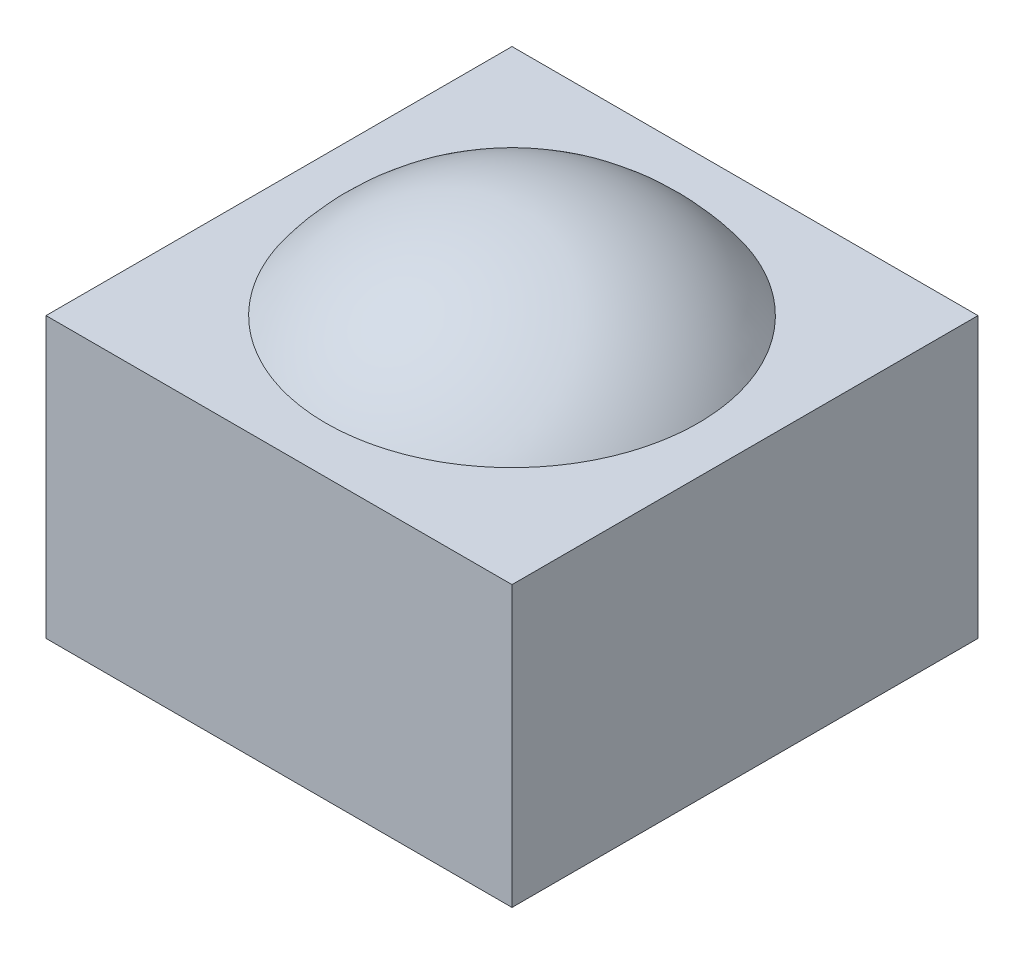
SolidWorks part; units mm, degrees
ref_plane "Ebene vorne" through (0, 0, 0) normal (0, 0, 1) x (1, 0, 0)
ref_plane "Ebene oben" through (0, 0, 0) normal (0, 1, 0) x (1, 0, 0)
ref_plane "Ebene rechts" through (0, 0, 0) normal (1, 0, 0) x (0, 0, -1)
sketch "Skizze1" plane through (0, 0, 0) normal (0, 0, 1) x (1, 0, 0)
  line L1 (0, 0) -> (0, 25)
  line L2 (0, 0) -> (0, -25)
  arc A0 (0, -25) -> (0, 25) centre (0, 0) cw
  dimension "D1" = 50
revolve "Rotation1" add sketch "Skizze1" angle 360 about L1
sketch "Skizze2" plane through (0, 0, 0) normal (0, 1, 0) x (1, 0, 0)
  line L1 (25, -25) -> (-25, -25)
  line L2 (25, -25) -> (25, 25)
  line L3 (25, 25) -> (-25, 25)
  line L4 (-25, -25) -> (-25, 25)
  line L5 (25, -25) -> (-25, 25) construction
  line L6 (25, 25) -> (-25, -25) construction
  circle A0 centre (0, 0) radius 25 construction
  point P0 (0, 0)
extrude "Aufsatz-Linear austragen1" add sketch "Skizze2" along normal mid plane 30 separate body
